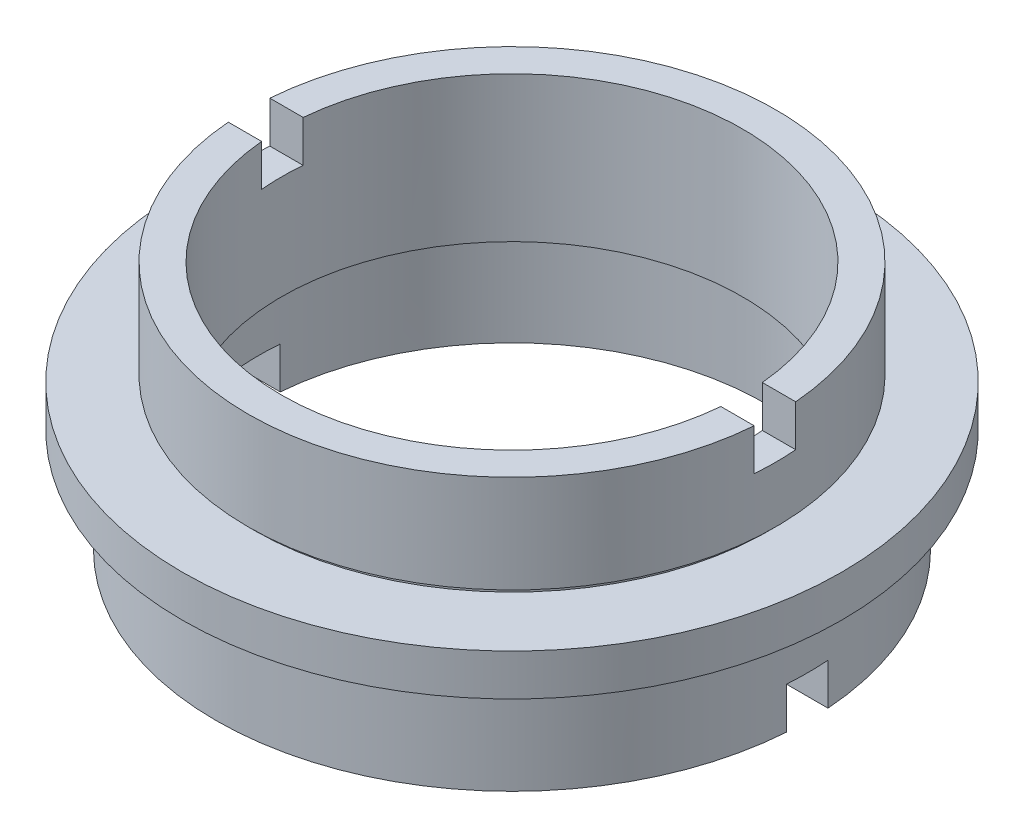
SolidWorks part; units mm, degrees
ref_plane "前视基准面" through (0, 0, 0) normal (0, 0, 1) x (1, 0, 0)
ref_plane "上视基准面" through (0, 0, 0) normal (0, 1, 0) x (1, 0, 0)
ref_plane "右视基准面" through (0, 0, 0) normal (1, 0, 0) x (0, 0, -1)
sketch "草图1" plane through (0, 0, 0) normal (0, 0, 1) x (1, 0, 0)
  line L0 (0, 22.6775) -> (0, 0) construction
  line L1 (-11.1, 12) -> (-12.7, 12)
  line L2 (-12.7, 12) -> (-12.7, 7.3)
  line L3 (-12.7, 7.3) -> (-12.4, 7.3)
  line L4 (-12.4, 7.3) -> (-12.4, 7)
  line L5 (-12.4, 7) -> (-15.875, 7)
  line L6 (-15.875, 7) -> (-15.875, 5)
  line L7 (-15.875, 5) -> (-13.75, 5)
  line L8 (-13.75, 5) -> (-13.75, 4)
  line L9 (-13.75, 4) -> (-14.25, 4)
  line L10 (-14.25, 4) -> (-14.25, 0)
  line L11 (-14.25, 0) -> (-12.2, 0)
  line L12 (-12.2, 0) -> (-12.2, 4.7)
  line L13 (-11.1, 5) -> (-12.7, 5)
  line L14 (-12.7, 5) -> (-12.7, 4.7)
  line L15 (-12.7, 4.7) -> (-12.2, 4.7)
  line L16 (-11.1, 12) -> (-11.1, 5)
  point P3 (-12.45, 4.7)
  point P5 (-15.875, 6)
  dimension "D2" = 1
  dimension "D3" = 0.3
  dimension "D4" = 5
  dimension "D5" = 5
  dimension "D6" = 12.7
  dimension "D7" = 15.875
  dimension "D8" = 14.25
  dimension "D9" = 13.75
  dimension "D10" = 12.4
  dimension "D11" = 12.2
  dimension "D12" = 0
  dimension "D13" = 12.7
  dimension "D14" = 11.1
  dimension "D15" = 12
  dimension "D16" = 7
  dimension "D17" = 0.3
revolve "旋转1" add sketch "草图1" angle 360 about L0
cosmetic thread "装饰螺纹线1"
cosmetic thread "装饰螺纹线2"
cosmetic thread "装饰螺纹线3"
cosmetic thread "装饰螺纹线4"
sketch "草图2" plane through (0, 0, 0) normal (1, 0, 0) x (0, 0, -1)
  line L0 (12.2, 12) -> (-12.2, 12) construction
  line L1 (-1, 13.594) -> (1, 13.594)
  line L2 (-1, 13.594) -> (-1, 10)
  line L3 (-1, 10) -> (1, 10)
  line L4 (1, 13.594) -> (1, 10)
  line L5 (-1, 2) -> (1, 2)
  line L6 (-1, 2) -> (-1, -4.6679)
  line L7 (-1, -4.6679) -> (1, -4.6679)
  line L8 (1, 2) -> (1, -4.6679)
  dimension "D1" = 2
  dimension "D2" = 1
  dimension "D3" = 2
  dimension "D4" = 1
  dimension "D5" = 2
  dimension "D6" = 2
extrude "切除-拉伸1" cut sketch "草图2" against normal mid plane 79
